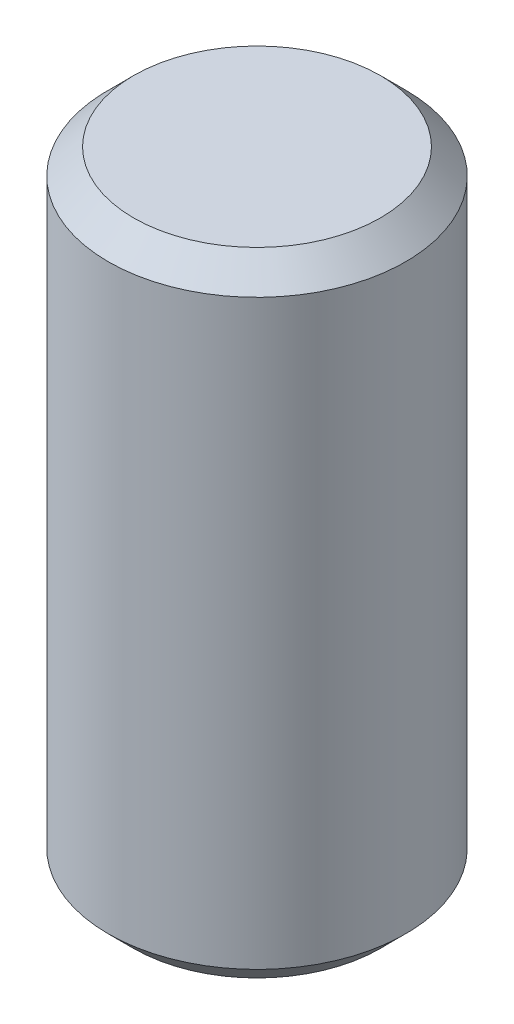
SolidWorks part; units mm, degrees
ref_plane "Front" through (0, 0, 0) normal (0, 0, 1) x (1, 0, 0)
ref_plane "Top" through (0, 0, 0) normal (0, 1, 0) x (1, 0, 0)
ref_plane "Right" through (0, 0, 0) normal (1, 0, 0) x (0, 0, -1)
sketch "Sketch1" plane through (0, 0, 0) normal (0, 0, 1) x (1, 0, 0)
  line L0 (0, 6.0802) -> (0, -6.0802) construction
  line L1 (0, -6.35) -> (2.9845, -6.35)
  line L2 (2.9845, -6.35) -> (2.9845, 6.35)
  line L3 (2.9845, 6.35) -> (0, 6.35)
  line L4 (0, 6.35) -> (0, -6.35)
  point P6 (0, 0)
  dimension "D1" = 5.969
  dimension "D2" = 12.7
revolve "Revolve1" add sketch "Sketch1" angle 360 about L0
chamfer "Chamfer1" distance 0.508 angle 45 2 edges at (0, -6.35, 2.9845) (0, 6.35, 2.9845)
